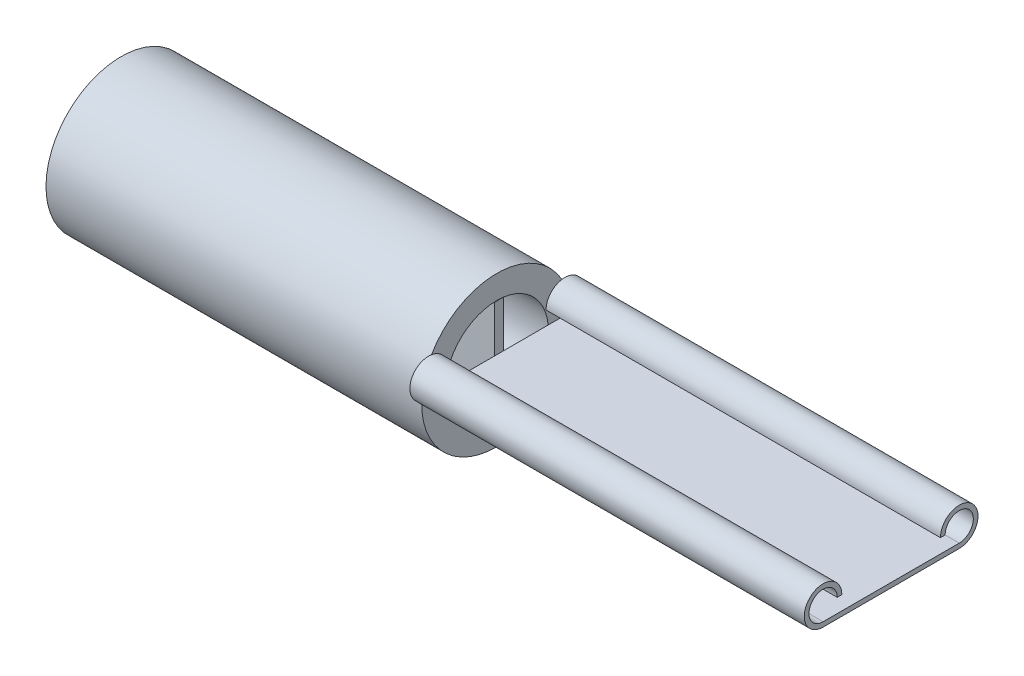
SolidWorks part; units mm, degrees
material "acero"
ref_plane "Alzado" through (0, 0, 0) normal (0, 0, 1) x (1, 0, 0)
ref_plane "Planta" through (0, 0, 0) normal (0, 1, 0) x (1, 0, 0)
ref_plane "Vista lateral" through (0, 0, 0) normal (1, 0, 0) x (0, 0, -1)
sketch "Sketch1" plane through (0, 0, 0) normal (1, 0, 0) x (0, 0, -1)
  circle A0 centre (0, 0) radius 1.1
  circle A1 centre (0, 0) radius 1.6
  dimension "D1" = 3.2
  dimension "D2" = 2.2
extrude "Boss-Extrude1" add sketch "Sketch1" along normal blind 8
sketch "Sketch2" plane through (8, 0, 0) normal (1, 0, 0) x (0, 0, -1)
  line L0 (-1.45, 0) -> (1.45, 0)
  line L1 (-1.45, 0.1) -> (1.45, 0.1)
  line L2 (-1.05, 0.4) -> (-1.15, 0.4)
  line L4 (1.05, 0.4) -> (1.15, 0.4)
  line L5 (0, 0) -> (0, 2.8936) construction
  line L6 (-1.45, 0) -> (1.85, 0) construction
  line L7 (-1.45, 0.1) -> (1.851, 0.1) construction
  arc A0 (-1.45, 0) -> (-1.05, 0.4) centre (-1.45, 0.4) cw
  arc A1 (1.45, 0.1) -> (1.15, 0.4) centre (1.45, 0.4) ccw
  arc A2 (1.45, 0) -> (1.05, 0.4) centre (1.45, 0.4) ccw
  arc A5 (-1.45, 0.1) -> (-1.15, 0.4) centre (-1.45, 0.4) cw
  arc A6 (1.851, 0.1) -> (1.5593, 0.3668) centre (1.8574, 0.3999) ccw construction
  arc A7 (1.85, 0) -> (1.4599, 0.3558) centre (1.8574, 0.3999) ccw construction
  point P7 (0, 0)
  point P27 (0, 0.1)
  dimension "D1" = 1.85
  dimension "D2" = 0.4
  dimension "D3" = 0.1
  dimension "D4" = 0.4
extrude "Boss-Extrude2" add sketch "Sketch2" along normal blind 8.4
sketch "Sketch3" plane through (0, 0, 0) normal (-1, 0, 0) x (0, 0, 1)
  line L1 (-0.1489, 1.0899) -> (0.0511, 1.0899)
  line L2 (-0.1489, 1.0899) -> (-0.1489, -1.0988)
  line L3 (-0.1489, -1.0988) -> (0.0511, -1.0988)
  line L4 (0.0511, 1.0899) -> (0.0511, -1.0988)
  circle A0 centre (0, 0) radius 1.1 construction
  dimension "D1" = 0.2
extrude "Boss-Extrude5" add sketch "Sketch3" against normal blind 8 separate body
